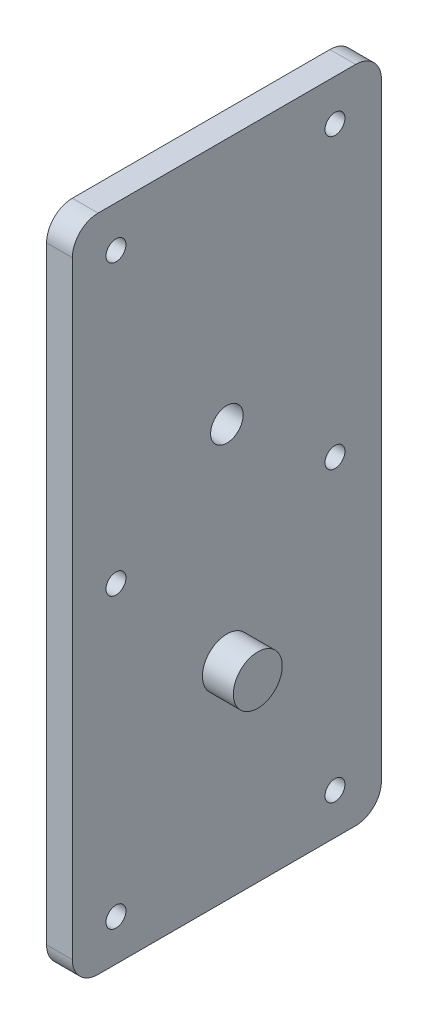
SolidWorks part; units mm, degrees
ref_plane "Front Plane" through (0, 0, 0) normal (0, 0, 1) x (1, 0, 0)
ref_plane "Top Plane" through (0, 0, 0) normal (0, 1, 0) x (1, 0, 0)
ref_plane "Right Plane" through (0, 0, 0) normal (1, 0, 0) x (0, 0, -1)
sketch "Sketch1" plane through (0, 0, 0) normal (1, 0, 0) x (0, 0, -1)
  line L6 (-31.75, -50.8) -> (31.75, -50.8)
  line L7 (-38.1, -44.45) -> (-38.1, 105.41)
  line L8 (-31.75, 111.76) -> (31.75, 111.76)
  line L9 (38.1, -44.45) -> (38.1, 105.41)
  line L10 (-38.1, -50.8) -> (38.1, 111.76) construction
  line L11 (-38.1, 111.76) -> (38.1, -50.8) construction
  arc A0 (0, -34.925) -> (33.7761, 8.8845) centre (0, 0) ccw construction
  arc A2 (33.7761, 8.8845) -> (-33.8552, 8.5779) centre (0, 0) ccw construction
  circle A5 centre (0, 0) radius 6.35 construction
  arc A6 (-33.8552, 8.5779) -> (0, -34.925) centre (0, 0) ccw construction
  arc A7 (-31.75, -50.8) -> (-38.1, -44.45) centre (-31.75, -44.45) cw
  arc A8 (31.75, -50.8) -> (38.1, -44.45) centre (31.75, -44.45) ccw
  arc A10 (-38.1, 105.41) -> (-31.75, 111.76) centre (-31.75, 105.41) cw
  arc A11 (38.1, 105.41) -> (31.75, 111.76) centre (31.75, 105.41) ccw
  point P10 (0, 30.48)
  dimension "D1" = 69.85
  dimension "D2" = 6.35
  dimension "D5" = 12.7
  dimension "D6" = 76.2
  dimension "D3" = 6.35
  dimension "D7" = 162.56
  dimension "D8" = 50.8
extrude "Right plate" add sketch "Sketch1" along normal blind 6.35
sketch "Sketch6" plane through (6.35, 0, 0) normal (1, 0, 0) x (0, 0, -1)
  circle A0 centre (0, 0) radius 9.525
  dimension "D1" = 19.05
extrude "Boss-Extrude4" [suppressed] add sketch "Sketch6" along normal blind 2.54
sketch "Sketch5" plane through (6.35, 0, 0) normal (1, 0, 0) x (0, 0, -1)
  circle A0 centre (0, 0) radius 6.0325
  dimension "D1" = 12.065
extrude "Spool post" add sketch "Sketch5" along normal blind 7.62
chamfer "Chamfer1" [suppressed] distance 5.969 angle 45
hole_wizard "1/4 Clearance Hole1" [suppressed] positions "Sketch10" profile "Sketch11" hole size "1/4" standard "ANSI Inch"
sketch "Sketch10" plane through (6.35, 0, 0) normal (1, 0, 0) x (0, 0, -1)
  line L1 (-38.1, -63.5) -> (38.1, -63.5) construction
  line L2 (-38.1, 139.7) -> (-38.1, -63.5) construction
  line L3 (-38.1, -50.8) -> (38.1, -50.8) construction
  line L4 (38.1, -63.5) -> (38.1, 139.7) construction
  line L6 (0, -50.8) -> (0, 139.7) construction
  line L7 (38.1, 139.7) -> (-38.1, 139.7) construction
  line L8 (25.4, 127) -> (-25.4, 127) construction
  point P3 (25.4, -50.8)
  point P6 (-25.4, -50.8)
  point P29 (-25.4, 127)
  point P31 (25.4, 127)
  dimension "D1" = 12.7
  dimension "D2" = 12.7
  dimension "D3" = 63.5
  dimension "D5" = 190.5
sketch "Sketch11" plane through (6.35, -50.8, -25.4) normal (0, 1, 0) x (0, 0, -1)
  line L0 (0, 0) -> (0, 6.35)
  line L1 (0, 6.35) -> (3.3782, 6.35)
  line L2 (3.3782, 6.35) -> (3.3782, 0)
  line L5 (3.3782, 0) -> (0, 0)
  line L11 (0, -6.35) -> (0, 107.95) construction
  dimension "Thru Hole Dia." = 6.7564
  dimension "Thru Hole Depth" = 6.35
sketch "Sketch12" [suppressed] plane through (0, 0, 0) normal (-1, 0, 0) x (0, 0, 1)
  circle A0 centre (-26.6465, -39.4028) radius 2.15 construction
  circle A1 centre (-26.6465, 31.7172) radius 2.15 construction
  circle A2 centre (-26.6465, 102.8372) radius 2.15 construction
  circle A3 centre (27.342, 102.8372) radius 2.15 construction
  circle A4 centre (27.342, 31.7172) radius 2.15 construction
  circle A5 centre (27.342, -39.4028) radius 2.15 construction
  circle A6 centre (-26.6465, -39.4028) radius 2.15
  circle A7 centre (-26.6465, 31.7172) radius 2.15
  circle A8 centre (-26.6465, 102.8372) radius 2.15
  circle A9 centre (27.342, 102.8372) radius 2.15
  circle A10 centre (27.342, 31.7172) radius 2.15
  circle A11 centre (27.342, -39.4028) radius 2.15
extrude "Cut-Extrude3" [suppressed] cut sketch "Sketch12" against normal blind 6.35
hole_wizard "O (0.316) Diameter Hole1" [suppressed] positions "Sketch13" profile "Sketch14" hole size "O" standard "ANSI Inch"
sketch "Sketch13" plane through (6.35, 0, 0) normal (1, 0, 0) x (0, 0, -1)
  line L0 (0, -63.5) -> (0, 76.2) construction
  line L1 (-38.1, -63.5) -> (38.1, -63.5) construction
  point P2 (0, 76.2)
  dimension "D1" = 139.7
sketch "Sketch14" plane through (6.35, 76.2, 0) normal (0, 1, 0) x (0, 0, -1)
  line L0 (0, 0) -> (0, 6.35)
  line L1 (0, 6.35) -> (4.0132, 6.35)
  line L2 (4.0132, 6.35) -> (4.0132, 0)
  line L5 (4.0132, 0) -> (0, 0)
  line L11 (0, -6.35) -> (0, 107.95) construction
  dimension "Thru Hole Dia." = 8.0264
  dimension "Thru Hole Depth" = 6.35
hole_wizard "#8 Clearance Hole1" positions "Sketch15" profile "Sketch16" hole size "#8" standard "ANSI Inch" end condition up to next
sketch "Sketch15" plane through (0, 0, 0) normal (-1, 0, 0) x (0, 0, 1)
  point P16 (-26.6465, 101.6003)
  point P19 (27.342, 101.6003)
  point P22 (27.342, 30.4803)
  point P25 (-26.6465, 30.4803)
  point P28 (-26.6465, -40.6397)
  point P31 (27.342, -40.6397)
  dimension "D1" = 53.9885
  dimension "D2" = 142.24
sketch "Sketch16" plane through (0, 101.6003, -26.6465) normal (0, 1, 0) x (0, 0, 1)
  line L0 (0, 0) -> (0, 6.35)
  line L1 (0, 6.35) -> (2.4574, 6.35)
  line L2 (2.4574, 6.35) -> (2.4574, 0)
  line L5 (2.4574, 0) -> (0, 0)
  line L11 (0, -6.35) -> (0, 107.95) construction
  dimension "Thru Hole Dia." = 4.9149
  dimension "Thru Hole Depth" = 6.35
hole_wizard "O (0.316) Diameter Hole3" positions "Sketch18" profile "Sketch17" hole size "O" standard "ANSI Inch" end condition through all
sketch "Sketch18" plane through (6.35, 0, 0) normal (1, 0, 0) x (0, 0, -1)
  point P0 (-675.1899, -31.3214)
  point P1 (0, 50.8)
sketch "Sketch17" plane through (6.35, -31.3214, 675.1899) normal (0, 1, 0) x (0, 0, -1)
  line L0 (0, 0) -> (0, 6.35)
  line L1 (0, 6.35) -> (4.0132, 6.35)
  line L2 (4.0132, 6.35) -> (4.0132, 0)
  line L5 (4.0132, 0) -> (0, 0)
  line L11 (0, -6.35) -> (0, 107.95) construction
  dimension "Thru Hole Dia." = 8.0264
  dimension "Thru Hole Depth" = 6.35
sketch "Sketch19" plane through (6.35, 0, 0) normal (1, 0, 0) x (0, 0, -1)
  line L0 (31.75, 111.76) -> (-31.75, 111.76) construction
  line L1 (-8.89, 96.52) -> (21.59, 96.52)
  line L2 (-8.89, 96.52) -> (-8.89, 81.28)
  line L3 (-8.89, 81.28) -> (21.59, 81.28)
  line L4 (21.59, 96.52) -> (21.59, 81.28)
  line L5 (38.1, -44.45) -> (38.1, 105.41) construction
  dimension "D1" = 15.24
  dimension "D2" = 30.48
  dimension "D3" = 15.24
  dimension "D4" = 16.51
extrude "Cut-Extrude4" [suppressed] cut sketch "Sketch19" against normal blind 1.905
chamfer "Chamfer2" [suppressed] distance 1.905 angle 45
